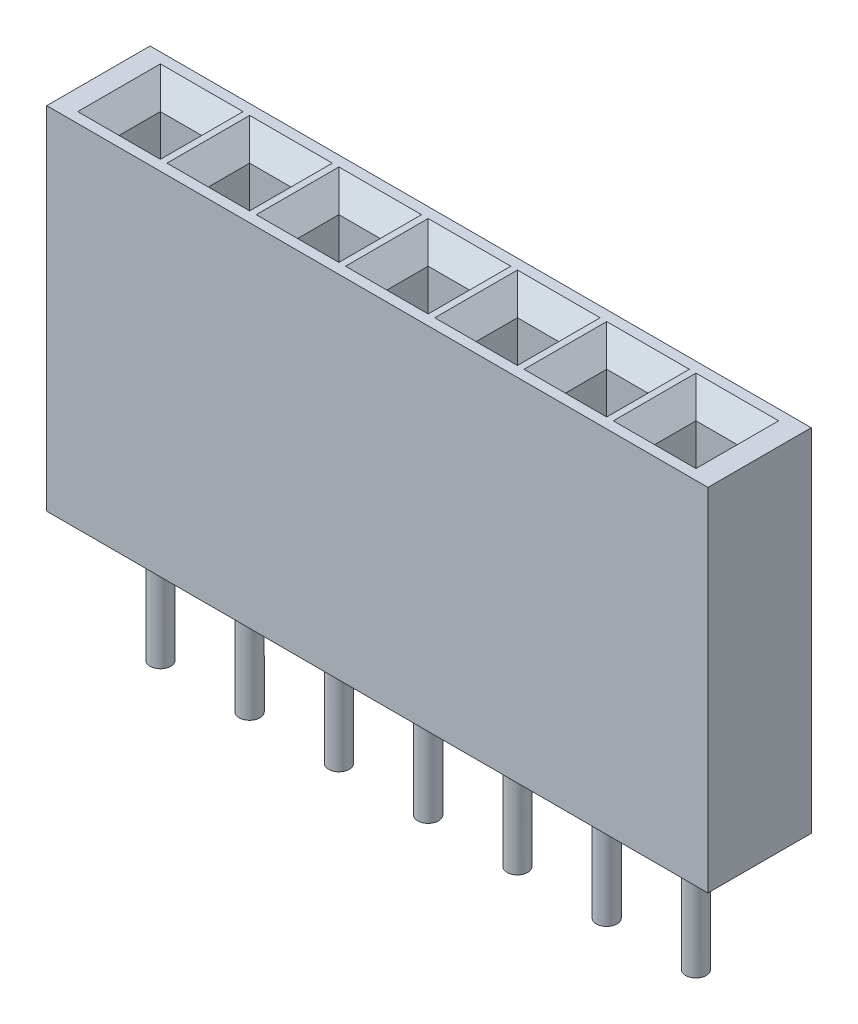
SolidWorks part; units mm, degrees
ref_plane "Front" through (0, 0, 0) normal (0, 0, 1) x (1, 0, 0)
ref_plane "Top" through (0, 0, 0) normal (0, 1, 0) x (1, 0, 0)
ref_plane "Right" through (0, 0, 0) normal (1, 0, 0) x (0, 0, -1)
sketch "Sketch1" plane through (0, 0, 0) normal (0, 1, 0) x (1, 0, 0)
  line L1 (0, 0) -> (16, 0)
  line L2 (0, 0) -> (0, 2.5)
  line L3 (0, 2.5) -> (16, 2.5)
  line L4 (16, 0) -> (16, 2.5)
  dimension "D1" = 2.5
  dimension "D2" = 16
extrude "Boss-Extrude1" add sketch "Sketch1" along normal blind 8.5
sketch "Sketch2" plane through (0, 8.5, 0) normal (0, 1, 0) x (1, 0, 0)
  line L0 (0, 1.25) -> (16, 1.25) construction
  line L1 (1, 1.75) -> (2, 1.75)
  line L2 (1, 1.75) -> (1, 0.75)
  line L3 (1, 0.75) -> (2, 0.75)
  line L4 (2, 1.75) -> (2, 0.75)
  line L5 (0, 2.5) -> (0, 0) construction
  line L6 (16, 0) -> (16, 2.5) construction
  line L7 (1, 1.25) -> (2, 1.25) construction
  line L8 (3.16, 1.75) -> (4.16, 1.75)
  line L9 (3.16, 1.75) -> (3.16, 0.75)
  line L10 (3.16, 0.75) -> (4.16, 0.75)
  line L11 (4.16, 1.75) -> (4.16, 0.75)
  line L12 (5.32, 1.75) -> (6.32, 1.75)
  line L13 (5.32, 1.75) -> (5.32, 0.75)
  line L14 (5.32, 0.75) -> (6.32, 0.75)
  line L15 (6.32, 1.75) -> (6.32, 0.75)
  line L16 (7.48, 1.75) -> (8.48, 1.75)
  line L17 (7.48, 1.75) -> (7.48, 0.75)
  line L18 (7.48, 0.75) -> (8.48, 0.75)
  line L19 (8.48, 1.75) -> (8.48, 0.75)
  line L20 (9.64, 1.75) -> (10.64, 1.75)
  line L21 (9.64, 1.75) -> (9.64, 0.75)
  line L22 (9.64, 0.75) -> (10.64, 0.75)
  line L23 (10.64, 1.75) -> (10.64, 0.75)
  line L24 (11.8, 1.75) -> (12.8, 1.75)
  line L25 (11.8, 1.75) -> (11.8, 0.75)
  line L26 (11.8, 0.75) -> (12.8, 0.75)
  line L27 (12.8, 1.75) -> (12.8, 0.75)
  line L28 (13.96, 1.75) -> (14.96, 1.75)
  line L29 (13.96, 1.75) -> (13.96, 0.75)
  line L30 (13.96, 0.75) -> (14.96, 0.75)
  line L31 (14.96, 1.75) -> (14.96, 0.75)
  dimension "D1" = 1
  dimension "D2" = 1
  dimension "D3" = 7
extrude "Cut-Extrude1" cut sketch "Sketch2" against normal blind 5
chamfer "Chamfer1" distance 0.5 angle 45 28 edges at (14.46, 8.5, -0.75) (14.96, 8.5, -1.25) (14.46, 8.5, -1.75) (13.96, 8.5, -1.25) (12.3, 8.5, -0.75) (12.8, 8.5, -1.25) (12.3, 8.5, -1.75) (11.8, 8.5, -1.25) (10.14, 8.5, -1.75) (10.64, 8.5, -1.25) (10.14, 8.5, -0.75) (9.64, 8.5, -1.25) (8.48, 8.5, -1.25) (7.98, 8.5, -0.75) (7.48, 8.5, -1.25) (7.98, 8.5, -1.75) (5.82, 8.5, -0.75) (6.32, 8.5, -1.25) (5.82, 8.5, -1.75) (5.32, 8.5, -1.25) (4.16, 8.5, -1.25) (3.66, 8.5, -0.75) (3.16, 8.5, -1.25) (3.66, 8.5, -1.75) (1.5, 8.5, -0.75) (2, 8.5, -1.25) (1.5, 8.5, -1.75) (1, 8.5, -1.25)
sketch "Sketch3" plane through (0, 3.5, 0) normal (0, 1, 0) x (1, 0, 0)
  line L0 (1, 0.75) -> (2, 1.75) construction
  line L1 (3.16, 0.75) -> (4.16, 1.75) construction
  line L2 (5.32, 0.75) -> (6.32, 1.75) construction
  line L3 (7.48, 0.75) -> (8.48, 1.75) construction
  line L4 (9.64, 0.75) -> (10.64, 1.75) construction
  line L5 (11.8, 0.75) -> (12.8, 1.75) construction
  line L6 (13.96, 0.75) -> (14.96, 1.75) construction
  circle A0 centre (1.5, 1.25) radius 0.25
  circle A1 centre (3.66, 1.25) radius 0.25
  circle A2 centre (5.82, 1.25) radius 0.25
  circle A3 centre (7.98, 1.25) radius 0.25
  circle A4 centre (10.14, 1.25) radius 0.25
  circle A5 centre (12.3, 1.25) radius 0.25
  circle A6 centre (14.46, 1.25) radius 0.25
  dimension "D1" = 0.5
extrude "Boss-Extrude2" add sketch "Sketch3" against normal blind 6.5
